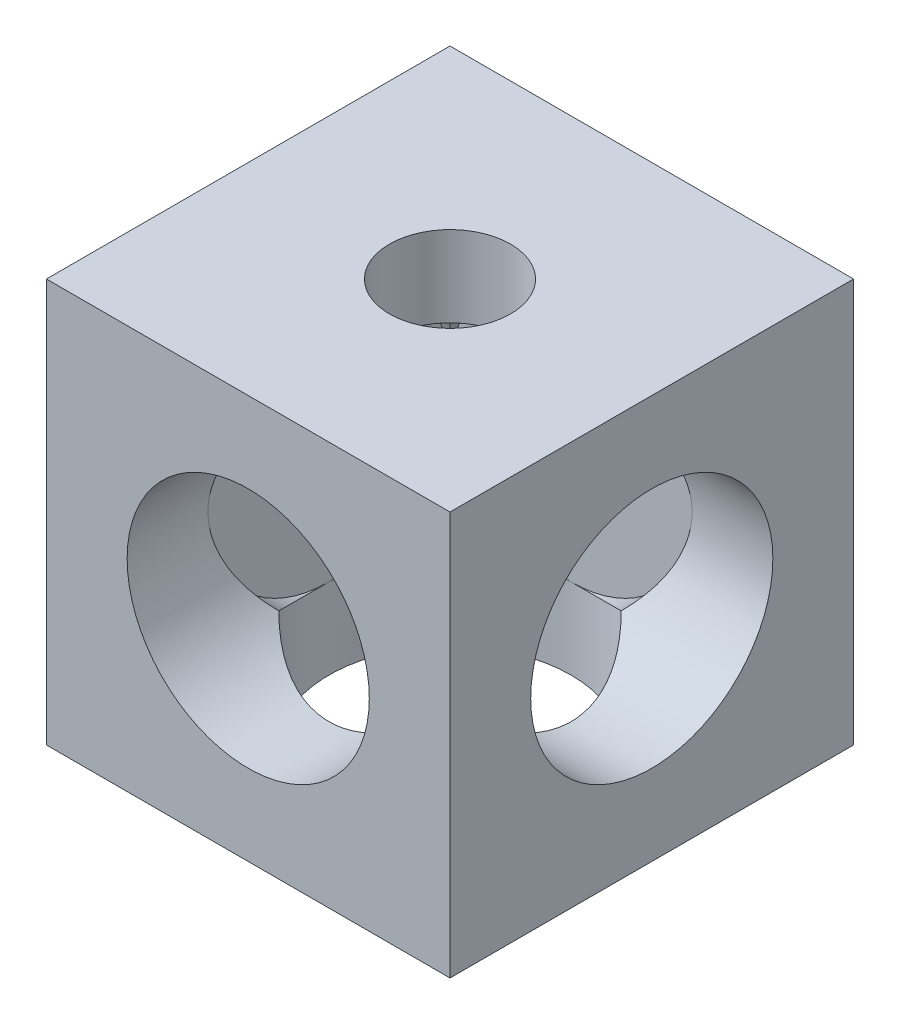
SolidWorks part; units mm, degrees
ref_plane "Front Plane" through (0, 0, 0) normal (0, 0, 1) x (1, 0, 0)
ref_plane "Top Plane" through (0, 0, 0) normal (0, 1, 0) x (1, 0, 0)
ref_plane "Right Plane" through (0, 0, 0) normal (1, 0, 0) x (0, 0, -1)
sketch "Esquisse1" plane through (0, 0, 0) normal (0, 0, 1) x (1, 0, 0)
  line L1 (0, 0) -> (10, 0)
  line L2 (0, 0) -> (0, 10)
  line L3 (0, 10) -> (10, 10)
  line L4 (10, 0) -> (10, 10)
  dimension "D1" = 10
extrude "Boss.-Extru.1" add sketch "Esquisse1" along normal blind 10
sketch "Esquisse2" plane through (0, 0, 10) normal (0, 0, 1) x (1, 0, 0)
  line L1 (10, 10) -> (0, 10) construction
  line L2 (0, 10) -> (0, 0) construction
  circle A0 centre (5, 5) radius 1.5
  point P2 (5, 5)
  point P3 (4.9951, 4.9829)
  point P4 (0, 0)
  point P6 (0, 0)
  point P9 (5, 10)
  point P11 (0, 5)
  dimension "D1" = 3
extrude "Enlèv. mat.-Extru.1" cut sketch "Esquisse2" against normal through all
sketch "Esquisse3" plane through (0, 0, 10) normal (0, 0, 1) x (1, 0, 0)
  circle A0 centre (5, 5) radius 3
  circle A1 centre (5, 5) radius 1.5 construction
  dimension "D1" = 6
extrude "Enlèv. mat.-Extru.2" cut sketch "Esquisse3" against normal blind 8
sketch "Esquisse4" plane through (10, 0, 0) normal (1, 0, 0) x (0, 0, -1)
  line L0 (-10, 10) -> (0, 10) construction
  line L1 (0, 0) -> (0, 10) construction
  circle A0 centre (-5, 5) radius 1.5
  point P4 (-5, 10)
  point P5 (0, 0)
  point P8 (0, 5)
  dimension "D1" = 3
extrude "Enlèv. mat.-Extru.3" cut sketch "Esquisse4" against normal through all
sketch "Esquisse5" plane through (10, 0, 0) normal (1, 0, 0) x (0, 0, -1)
  circle A0 centre (-5, 5) radius 3
  circle A1 centre (-5, 5) radius 1.5 construction
  point P2 (0, 0)
  dimension "D1" = 6
extrude "Enlèv. mat.-Extru.4" cut sketch "Esquisse5" against normal blind 8
sketch "Esquisse6" plane through (0, 0, 0) normal (0, -1, 0) x (1, 0, 0)
  line L1 (0, 0) -> (10, 0) construction
  line L4 (10, 10) -> (10, 0) construction
  circle A0 centre (5, 5) radius 1.5
  point P2 (0, 0)
  point P5 (0, 0)
  point P6 (4.3963, 4.228)
  point P7 (0, 0)
  point P8 (0, 0)
  point P9 (0, 0)
  point P10 (0, 0)
  point P12 (0, 0)
  point P13 (5, 0)
  point P15 (0, 0)
  point P16 (0, 0)
  point P17 (10, 5)
  dimension "D1" = 3
extrude "Enlèv. mat.-Extru.5" cut sketch "Esquisse6" against normal through all
sketch "Esquisse7" plane through (0, 0, 0) normal (0, -1, 0) x (-1, 0, 0)
  circle A0 centre (-5, -5) radius 3
  circle A1 centre (-5, -5) radius 1.5 construction
  point P2 (-4.7804, -4.8784)
  dimension "D1" = 6
extrude "Enlèv. mat.-Extru.6" cut sketch "Esquisse7" against normal blind 8
